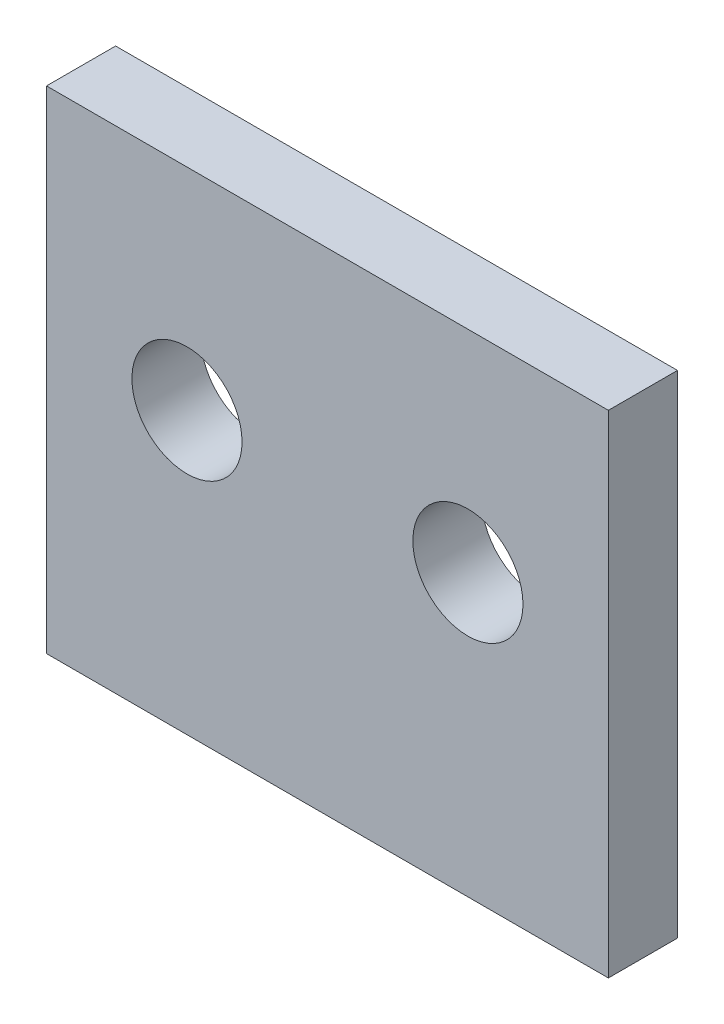
SolidWorks part; units mm, degrees
ref_plane "Front Plane" through (0, 0, 0) normal (0, 0, 1) x (1, 0, 0)
ref_plane "Top Plane" through (0, 0, 0) normal (0, 1, 0) x (1, 0, 0)
ref_plane "Right Plane" through (0, 0, 0) normal (1, 0, 0) x (0, 0, -1)
sketch "Sketch1" plane through (0, 0, 0) normal (0, 0, 1) x (1, 0, 0)
  line L1 (25.4, 248.92) -> (0, 248.92)
  line L2 (25.4, 248.92) -> (25.4, 226.695)
  line L3 (25.4, 226.695) -> (0, 226.695)
  line L4 (0, 248.92) -> (0, 226.695)
  circle A2 centre (6.35, 239.395) radius 2.4892
  circle A3 centre (19.05, 239.395) radius 2.4892
extrude "Boss-Extrude1" add sketch "Sketch1" along normal blind 3.175 contours L1 L4 L3 L2 A3 A2
sketch "Sketch2" plane through (0, 0, 0) normal (-1, 0, 0) x (0, 0, 1)
  line L0 (3.175, 248.92) -> (0, 248.92) construction
  line L1 (0, 226.695) -> (0.0508, 226.695)
  line L2 (0, 226.695) -> (0, 248.92)
  line L3 (0, 248.92) -> (0.0508, 248.92)
  line L4 (0.0508, 226.695) -> (0.0508, 248.92)
  dimension "D1" = 0.0508
extrude "Cut-Extrude1" cut sketch "Sketch2" against normal through all
equation "\"Thick\"= \"in\""
